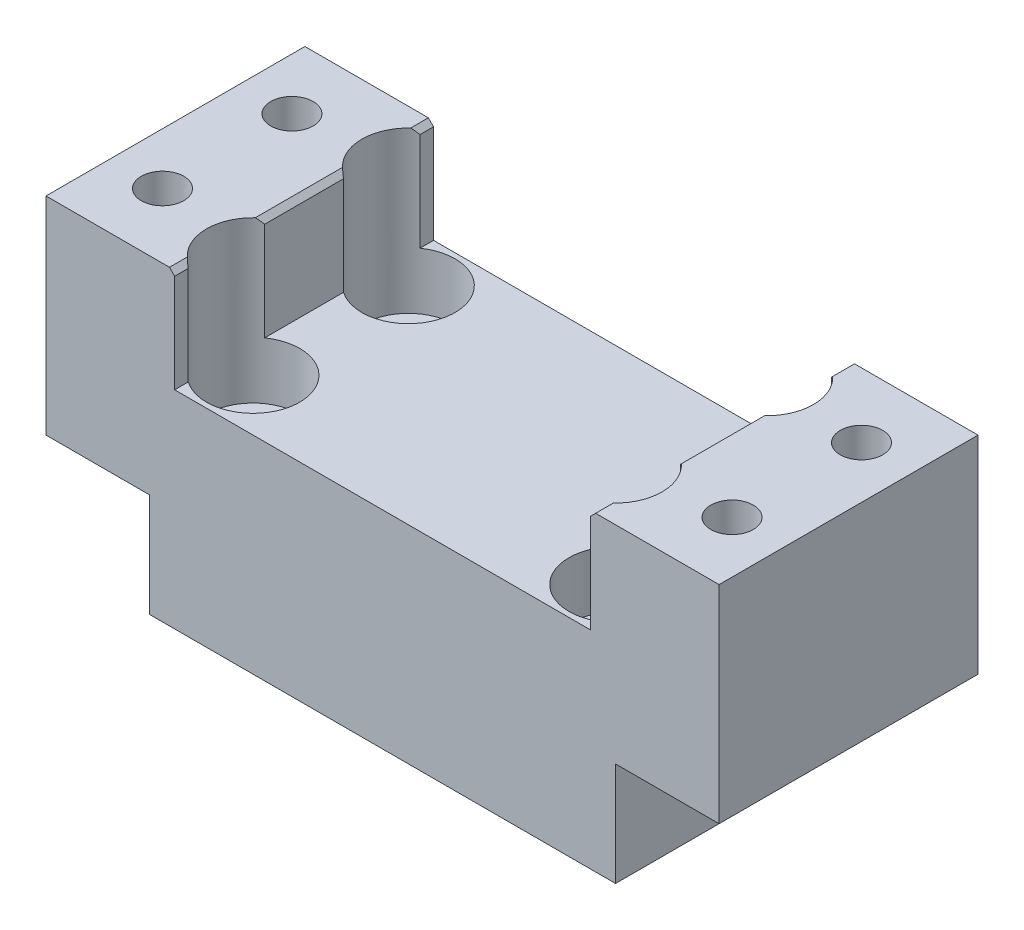
SolidWorks part; units mm, degrees
ref_plane "Спереди" through (0, 0, 0) normal (0, 0, 1) x (1, 0, 0)
ref_plane "Сверху" through (0, 0, 0) normal (0, 1, 0) x (1, 0, 0)
ref_plane "Справа" through (0, 0, 0) normal (1, 0, 0) x (0, 0, -1)
sketch "Sketch1" plane through (0, 0, 0) normal (0, 1, 0) x (1, 0, 0)
  line L1 (65, -25) -> (-65, -25)
  line L2 (65, -25) -> (65, 25)
  line L3 (65, 25) -> (-65, 25)
  line L4 (-65, -25) -> (-65, 25)
  line L5 (65, -25) -> (-65, 25) construction
  line L6 (65, 25) -> (-65, -25) construction
  point P0 (0, 0)
  dimension "D1" = 130
  dimension "D2" = 50
extrude "Boss-Extrude1" add sketch "Sketch1" along normal blind 60
sketch "Sketch2" plane through (0, 0, 25) normal (0, 0, 1) x (1, 0, 0)
  line L0 (-65, 60) -> (65, 60) construction
  line L1 (40.15, 80) -> (-40.15, 80)
  line L2 (40.15, 80) -> (40.15, 40)
  line L3 (40.15, 40) -> (-40.15, 40)
  line L4 (-40.15, 80) -> (-40.15, 40)
  line L5 (40.15, 80) -> (-40.15, 40) construction
  line L6 (40.15, 40) -> (-40.15, 80) construction
  point P0 (0, 60)
  dimension "D1" = 80.3
  dimension "D2" = 40
extrude "Cut-Extrude1" cut sketch "Sketch2" against normal through all
sketch "Sketch3" plane through (0, 0, 0) normal (0, -1, 0) x (1, 0, 0)
  line L1 (-35, -15) -> (35, -15) construction
  line L2 (-35, -15) -> (-35, 15) construction
  line L3 (-35, 15) -> (35, 15) construction
  line L4 (35, -15) -> (35, 15) construction
  line L5 (-35, -15) -> (35, 15) construction
  line L6 (-35, 15) -> (35, -15) construction
  circle A0 centre (-35, 15) radius 4.1
  circle A1 centre (-35, -15) radius 4.1
  circle A2 centre (35, -14.2173) radius 4.1
  circle A3 centre (35, 15) radius 4.1
  point P0 (0, 0)
  point P11 (35, 0)
  dimension "D3" = 8.2
  dimension "D1" = 30
  dimension "D2" = 70
extrude "Cut-Extrude2" cut sketch "Sketch3" against normal through all
sketch "Sketch4" plane through (0, 0, 0) normal (0, -1, 0) x (1, 0, 0)
  circle A0 centre (35, 15) radius 8
  circle A1 centre (35, -14.2173) radius 8
  circle A2 centre (-35, 15) radius 8
  circle A3 centre (-35, -15) radius 8
  dimension "D1" = 16
extrude "Cut-Extrude3" cut sketch "Sketch4" against normal blind 7
chamfer "Chamfer1" distance 1 angle 45 2 edges at (-40.15, 60, 0) (40.15, 60, 0)
sketch "Sketch5" plane through (0, 0, 0) normal (0, -1, 0) x (1, 0, 0)
  line L0 (65, -25) -> (-65, -25) construction
  line L1 (-45, 25) -> (45, 25)
  line L2 (-45, 25) -> (-45, -25)
  line L3 (-45, -25) -> (45, -25)
  line L4 (45, 25) -> (45, -25)
  line L5 (-45, 25) -> (45, -25) construction
  line L6 (-45, -25) -> (45, 25) construction
  point P0 (0, 0)
  dimension "D1" = 90
extrude "Cut-Extrude4" cut sketch "Sketch5" against normal blind 20 flip side to cut
sketch "Sketch6" plane through (0, 20, 0) normal (0, -1, 0) x (1, 0, 0)
  line L0 (55, -25) -> (55, 25) construction
  line L1 (45, -25) -> (65, -25) construction
  line L2 (65, 25) -> (45, 25) construction
  line L3 (-55, -25) -> (-55, 25) construction
  line L4 (-65, -25) -> (-45, -25) construction
  line L5 (-45, 25) -> (-65, 25) construction
  line L7 (-55, 12.5) -> (55, 12.5) construction
  line L8 (-55, 12.5) -> (-55, -12.5) construction
  line L9 (-55, -12.5) -> (55, -12.5) construction
  line L10 (55, 12.5) -> (55, -12.5) construction
  line L11 (-55, 12.5) -> (55, -12.5) construction
  line L12 (-55, -12.5) -> (55, 12.5) construction
  circle A0 centre (55, -12.5) radius 4.1
  circle A1 centre (55, 12.5) radius 4.1
  circle A2 centre (-55, -12.5) radius 4.1
  circle A3 centre (-55, 12.5) radius 4.1
  point P12 (0, 0)
  point P14 (0, 0)
  point P16 (0, 0)
  point P20 (0, 0)
  point P26 (0, 0)
  dimension "D2" = 8.2
  dimension "D1" = 25
extrude "Cut-Extrude5" cut sketch "Sketch6" against normal through all
sketch "Sketch7" plane through (0, 40, 0) normal (0, 1, 0) x (1, 0, 0)
  circle A0 centre (35, -15) radius 9
  circle A1 centre (-35, -15) radius 9
  circle A2 centre (35, 14.2173) radius 9
  circle A3 centre (-35, 15) radius 9
  dimension "D1" = 18
extrude "Cut-Extrude6" cut sketch "Sketch7" along normal through all and the other way blind 11
